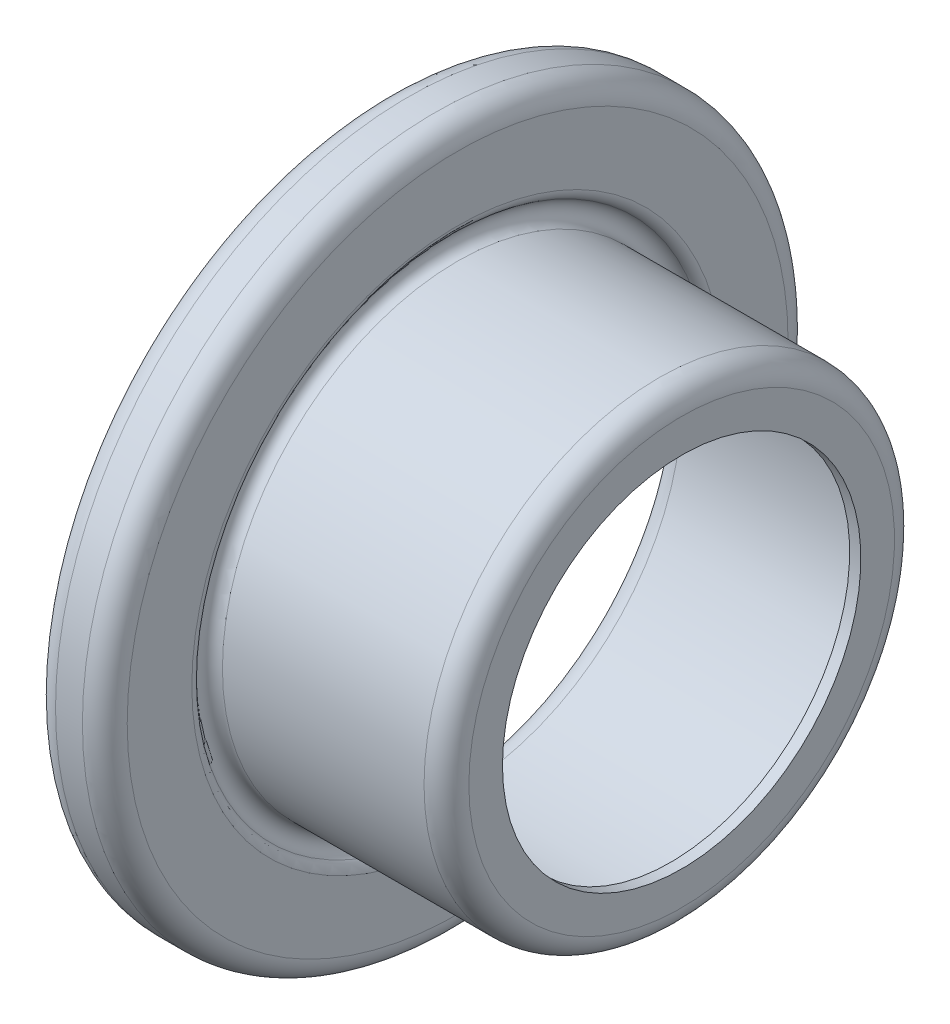
SolidWorks part; units mm, degrees
ref_plane "Face" through (0, 0, 0) normal (0, 0, 1) x (1, 0, 0)
ref_plane "Dessus" through (0, 0, 0) normal (0, 1, 0) x (1, 0, 0)
ref_plane "Droite" through (0, 0, 0) normal (1, 0, 0) x (0, 0, -1)
sketch "Esquisse1" plane through (0, 0, 0) normal (0, 0, 1) x (1, 0, 0)
  line L0 (-70, 0) -> (24, 0) construction
  line L1 (0, 8) -> (0, 9.5)
  line L2 (-1, 10.5) -> (-10, 10.5)
  line L3 (-10, 11.866) -> (-10, 14.75)
  line L4 (-11, 15.75) -> (-12.2, 15.75)
  line L5 (-13.2, 14.75) -> (-13.2, 14)
  arc A0 (-1, 10.5) -> (0, 9.5) centre (-1, 9.5) cw
  arc A1 (-11, 15.75) -> (-10, 14.75) centre (-11, 14.75) cw
  arc A2 (-10, 10.5) -> (-10.25, 11.433) centre (-10, 11) cw
  arc A3 (-10, 11.866) -> (-10.25, 11.433) centre (-10.5, 11.866) cw
  arc A4 (-13.2, 14.75) -> (-12.2, 15.75) centre (-12.2, 14.75) cw
  dimension "D6" = 1
  dimension "D7" = 1
  dimension "D8" = 0.5
  dimension "D10" = 0.5
  dimension "D5" = 1
  dimension "D1" = 16
  dimension "D2" = 21
  dimension "D3" = 31.5
  dimension "D4" = 10
  dimension "D11" = 28
  dimension "D12" = 13.2
revolve "Base-Révol.-Mince" add sketch "Esquisse1" angle 360 about L0
sketch "Esquisse2" plane through (0, 0, 0) normal (0, 0, 1) x (1, 0, 0)
  line L0 (4.1, 0) -> (-19.8, 0) construction
  line L1 (-70, 0) -> (24, 0) construction
  line L2 (-12.9, 14) -> (-12.9, 14.75)
  line L3 (-11, 15.25) -> (-12.2, 15.25) construction
  line L4 (-11, 15.25) -> (-12.4, 15.25)
  line L5 (-12.7, 14) -> (-13.2, 14) construction
  line L6 (-12.7, 14) -> (-12.9, 14)
  line L7 (-12.7, 14) -> (-12.7, 14.5307)
  line L8 (-11, 15.25) -> (-12.2868, 15.0231)
  arc A0 (-12.4, 15.25) -> (-12.9, 14.75) centre (-12.4, 14.75) ccw
  arc A1 (-12.2868, 15.0231) -> (-12.7, 14.5307) centre (-12.2, 14.5307) ccw
  dimension "D2" = 0.5
  dimension "D3" = 10
  dimension "D4" = 0.5
  dimension "D1" = 0.2
revolve "Enlèvement de matière-Révolution1" cut sketch "Esquisse2" angle 360 about L0
